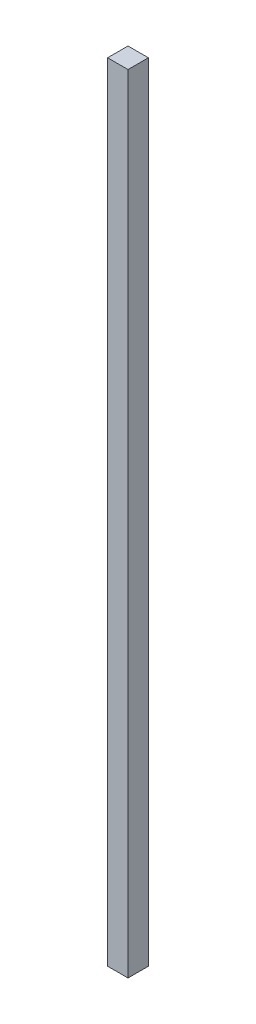
SolidWorks part; units mm, degrees
ref_plane "Front Plane" through (0, 0, 0) normal (0, 0, 1) x (1, 0, 0)
ref_plane "Top Plane" through (0, 0, 0) normal (0, 1, 0) x (1, 0, 0)
ref_plane "Right Plane" through (0, 0, 0) normal (1, 0, 0) x (0, 0, -1)
sketch "Sketch1" plane through (0, 0, 0) normal (0, 1, 0) x (1, 0, 0)
  line L1 (0, 0) -> (12, 0)
  line L2 (0, 0) -> (0, 12)
  line L3 (0, 12) -> (12, 12)
  line L4 (12, 0) -> (12, 12)
  dimension "D1" = 12
  dimension "D2" = 12
extrude "Boss-Extrude1" add sketch "Sketch1" along normal blind 463
